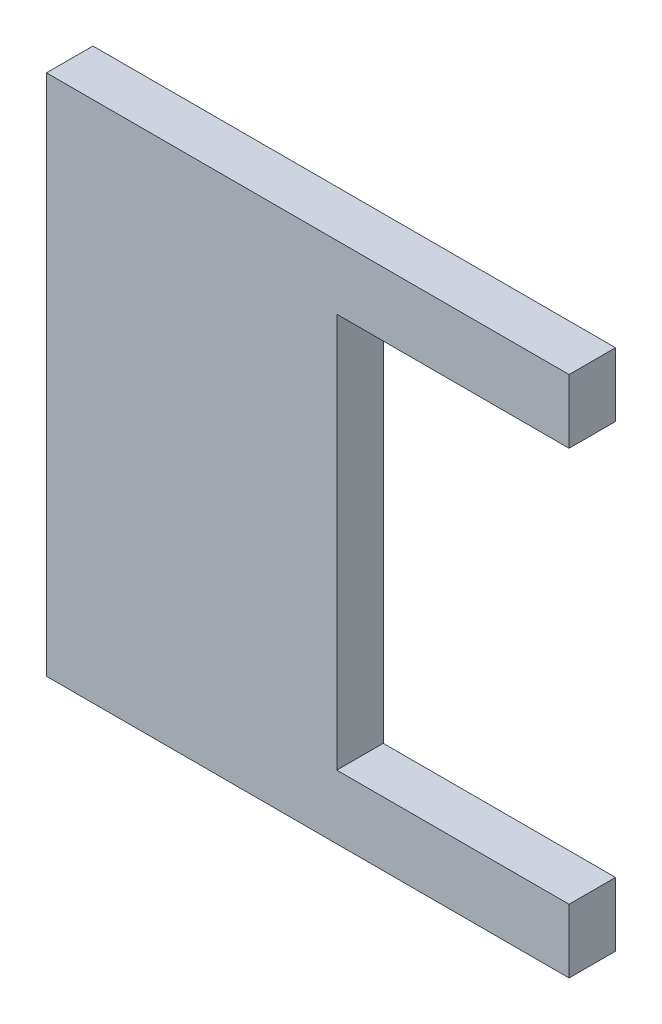
SolidWorks part; units mm, degrees
ref_plane "Přední rovina" through (0, 0, 0) normal (0, 0, 1) x (1, 0, 0)
ref_plane "Horní rovina" through (0, 0, 0) normal (0, 1, 0) x (1, 0, 0)
ref_plane "Pravá rovina" through (0, 0, 0) normal (1, 0, 0) x (0, 0, -1)
sketch "Skica1" plane through (0, 0, 0) normal (0, 0, 1) x (1, 0, 0)
  line L0 (0, 0) -> (0, 90)
  line L1 (0, 90) -> (90, 90)
  line L2 (90, 90) -> (90, 79)
  line L3 (90, 79) -> (50, 79)
  line L4 (50, 79) -> (50, 11)
  line L5 (50, 11) -> (90, 11)
  line L6 (90, 11) -> (90, 0)
  line L7 (90, 0) -> (0, 0)
  dimension "D1" = 90
  dimension "D2" = 90
  dimension "D3" = 90
  dimension "D4" = 11
  dimension "D5" = 11
  dimension "D6" = 40
extrude "Přidat vysunutím1" add sketch "Skica1" along normal blind 8
